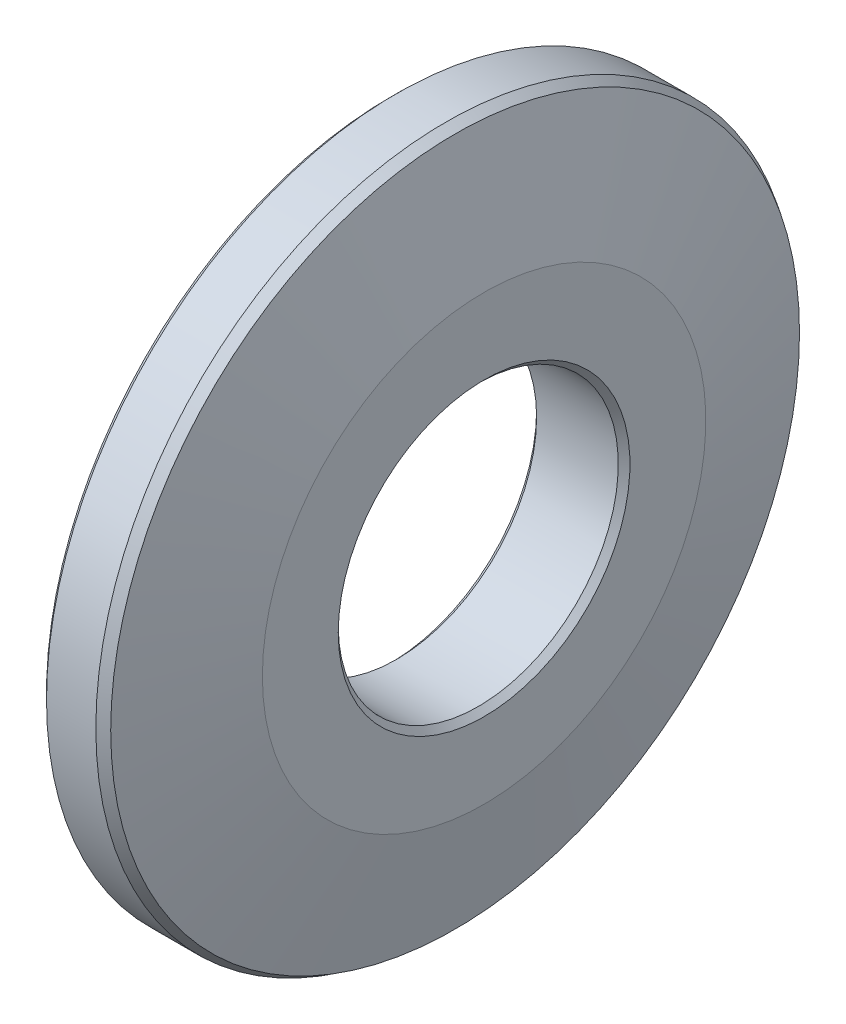
SolidWorks part; units mm, degrees
material "2024-T3"
ref_plane "Front Plane" through (0, 0, 0) normal (0, 0, 1) x (1, 0, 0)
ref_plane "Top Plane" through (0, 0, 0) normal (0, 1, 0) x (1, 0, 0)
ref_plane "Right Plane" through (0, 0, 0) normal (1, 0, 0) x (0, 0, -1)
sketch "Sketch1" plane through (0, 0, 0) normal (0, 1, 0) x (1, 0, 0)
  line L0 (2.7, 15) -> (4, 9.5)
  line L1 (0, 6) -> (4, 6)
  line L2 (0, 6) -> (0, 15)
  line L3 (0, 15) -> (2.7, 15)
  line L4 (4, 6) -> (4, 9.5)
  line L5 (0, 0) -> (11.2279, 0) construction
  dimension "D1" = 30
  dimension "D2" = 12
  dimension "D3" = 4
  dimension "D4" = 2.7
  dimension "D5" = 19
revolve "Revolve1" add sketch "Sketch1" angle 360 about L5
chamfer "Chamfer1" distance 0.25 angle 45 4 edges at (2.7, 0, 15) (0, 0, 15) (0, 0, 6) (4, 0, 6)
